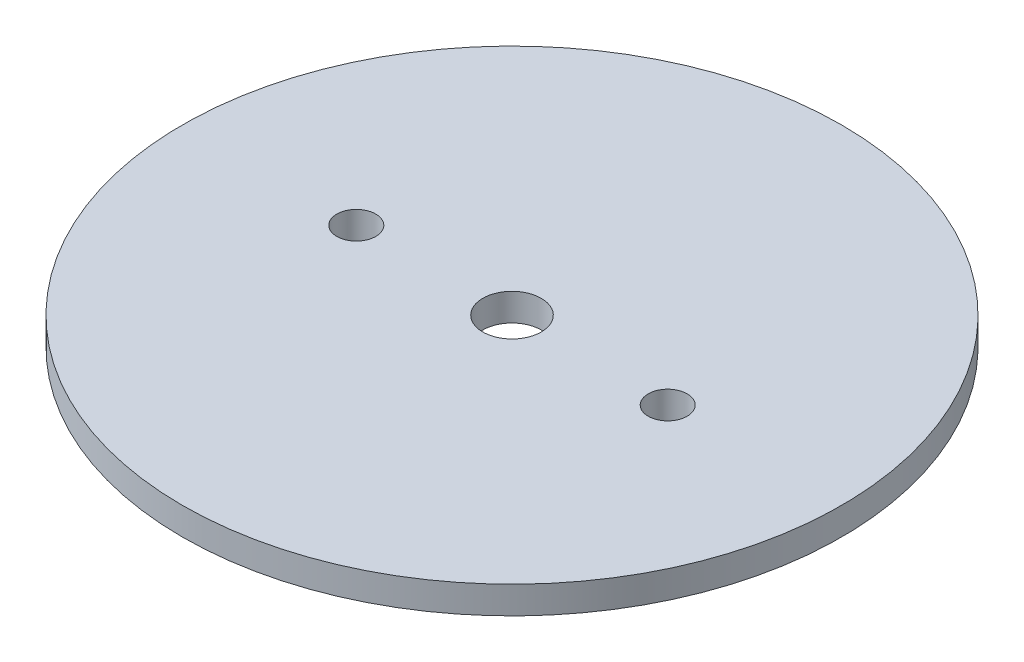
SolidWorks part; units mm, degrees
ref_plane "Front Plane" through (0, 0, 0) normal (0, 0, 1) x (1, 0, 0)
ref_plane "Top Plane" through (0, 0, 0) normal (0, 1, 0) x (1, 0, 0)
ref_plane "Right Plane" through (0, 0, 0) normal (1, 0, 0) x (0, 0, -1)
sketch "Sketch1" plane through (0, 0, 0) normal (0, 1, 0) x (1, 0, 0)
  circle A0 centre (0, 0) radius 38.1
  dimension "D1" = 76.2
extrude "Boss-Extrude1" add sketch "Sketch1" along normal mid plane 3.175
hole_wizard "M4 Clearance Hole1" positions "Sketch2" profile "Sketch3" hole size "M4" standard "ANSI Metric" end condition through all
sketch "Sketch2" plane through (0, -1.5875, 0) normal (0, -1, 0) x (-1, 0, 0)
  circle A0 centre (-18, 0) radius 2.85 construction
  circle A1 centre (18, 0) radius 2.85 construction
  point P0 (-18, 0)
  point P2 (18, 0)
sketch "Sketch3" plane through (18, -1.5875, 0) normal (1, 0, 0) x (0, 0, -1)
  line L0 (0, 0) -> (0, 3.175)
  line L1 (0, 3.175) -> (2.25, 3.175)
  line L2 (2.25, 3.175) -> (2.25, 0)
  line L5 (2.25, 0) -> (0, 0)
  line L11 (0, -6.35) -> (0, 107.95) construction
  dimension "Thru Hole Dia." = 4.5
  dimension "Thru Hole Depth" = 3.175
sketch "Sketch4" plane through (0, -1.5875, 0) normal (0, -1, 0) x (1, 0, 0)
  circle A2 centre (0, 0) radius 3.3782
  dimension "D1" = 6.7564
extrude "Cut-Extrude1" cut sketch "Sketch4" against normal through all
